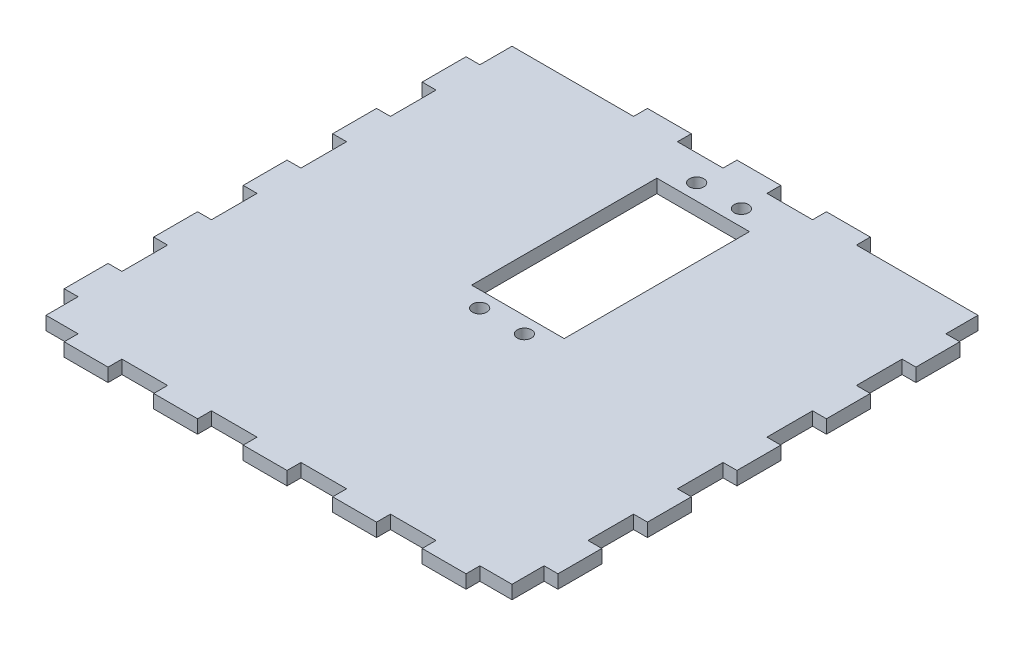
SolidWorks part; units mm, degrees
ref_plane "Front Plane" through (0, 0, 0) normal (0, 0, 1) x (1, 0, 0)
ref_plane "Top Plane" through (0, 0, 0) normal (0, 1, 0) x (1, 0, 0)
ref_plane "Right Plane" through (0, 0, 0) normal (1, 0, 0) x (0, 0, -1)
sketch "Sketch1" plane through (0, 0, 0) normal (0, 1, 0) x (1, 0, 0)
  line L0 (0, 0) -> (0, 21) construction
  line L1 (-10.05, 30.75) -> (-10.05, -10.05) construction
  line L2 (-10.05, -10.05) -> (10.05, -10.05) construction
  line L3 (10.05, 30.75) -> (10.05, -10.05) construction
  line L4 (-10.05, 30.75) -> (10.05, 30.75) construction
  line L5 (-10.05, 30.75) -> (-10.05, -10.05) construction
  line L6 (-10.05, -10.05) -> (10.05, -10.05) construction
  line L7 (10.05, 30.75) -> (10.05, -10.05) construction
  line L8 (-10.05, 30.75) -> (10.05, 30.75) construction
  line L9 (-10.35, 31.05) -> (10.35, 31.05)
  line L10 (10.35, 31.05) -> (10.35, -10.35)
  line L11 (-10.35, -10.35) -> (10.35, -10.35)
  line L12 (-10.35, 31.05) -> (-10.35, -10.35)
  line L13 (55.1722, 43.5014) -> (55.1722, -66.843) construction
  line L14 (55.1722, 43.5014) -> (55.1722, -66.843)
  line L15 (-55.1722, 43.5014) -> (-55.1722, -66.843) construction
  line L16 (-55.1722, 43.5014) -> (-55.1722, -66.843)
  line L17 (-55.1722, -66.843) -> (55.1722, -66.843) construction
  line L18 (-55.1722, -66.843) -> (55.1722, -66.843)
  line L20 (-55.1722, 43.5014) -> (55.1722, 43.5014) construction
  line L21 (-55.1722, 43.5014) -> (55.1722, 43.5014)
  circle A0 centre (0, 0) radius 21 construction
  circle A1 centre (0, 0) radius 21 construction
  circle A2 centre (-5, -13.9) radius 2 construction
  circle A3 centre (5, -13.9) radius 2 construction
  circle A4 centre (-5, 34.6) radius 2 construction
  circle A5 centre (5, 34.6) radius 2 construction
  circle A6 centre (5, -13.9) radius 2 construction
  circle A7 centre (-5, -13.9) radius 2 construction
  circle A8 centre (-5, 34.6) radius 2 construction
  circle A9 centre (5, 34.6) radius 2 construction
  circle A10 centre (-5, 34.6) radius 1.6
  circle A11 centre (5, 34.6) radius 1.6
  circle A12 centre (5, -13.9) radius 1.6
  circle A13 centre (-5, -13.9) radius 1.6
  dimension "D2" = 3.2
  dimension "D1" = 0.3
extrude "Boss-Extrude1" add sketch "Sketch1" along normal up to vertex (3 mm away)
sketch "Sketch2" plane through (0, 0, 0) normal (0, 1, 0) x (1, 0, 0)
  line L0 (-55.1722, -6.6708) -> (-52.1722, -6.6708)
  line L1 (-55.1722, -16.6708) -> (-52.1722, -16.6708)
  line L2 (-55.1722, 3.3292) -> (-52.1722, 3.3292)
  line L3 (-55.1722, 13.3292) -> (-52.1722, 13.3292)
  line L4 (-55.1722, 43.5014) -> (-55.1722, -66.843) construction
  line L5 (-55.1722, 43.5014) -> (55.1722, 43.5014)
  line L6 (-55.1722, 43.5014) -> (-55.1722, -66.843)
  line L7 (-55.1722, -66.843) -> (55.1722, -66.843)
  line L8 (55.1722, 43.5014) -> (55.1722, -66.843)
  line L9 (-55.1722, 43.5014) -> (55.1722, 43.5014) construction
  line L10 (55.1722, 43.5014) -> (55.1722, -66.843) construction
  line L11 (-55.1722, -66.843) -> (55.1722, -66.843) construction
  line L12 (0, -11.6708) -> (0, 43.5014) construction
  line L13 (-55.1722, -11.6708) -> (0, -11.6708) construction
  line L14 (-52.1722, 40.5014) -> (-52.1722, -63.843) construction
  line L15 (-52.1722, -63.843) -> (52.1722, -63.843) construction
  line L16 (52.1722, -63.843) -> (52.1722, 40.5014) construction
  line L17 (52.1722, 40.5014) -> (-52.1722, 40.5014) construction
  line L18 (-55.1722, 43.5014) -> (0, -11.6708) construction
  line L19 (-52.1722, -63.843) -> (-55.1722, -63.843) construction
  line L20 (-32.0585, 80.0877) -> (-35.0585, 80.0877) construction
  line L21 (-53.6722, -6.6708) -> (-53.6722, -16.6708) construction
  line L22 (-53.6722, -6.6708) -> (-53.6722, 3.3292) construction
  line L23 (-53.6722, 3.3292) -> (-53.6722, 13.3292) construction
  line L24 (-55.1722, 23.3292) -> (-52.1722, 23.3292)
  line L25 (-55.1722, 33.3292) -> (-52.1722, 33.3292)
  line L26 (-53.6722, 13.3292) -> (-53.6722, 23.3292) construction
  line L27 (-53.6722, 23.3292) -> (-53.6722, 33.3292) construction
  line L28 (-55.1722, -16.6708) -> (-52.1722, -16.6708)
  line L29 (-55.1722, -26.6708) -> (-52.1722, -26.6708)
  line L30 (-55.1722, -36.6708) -> (-52.1722, -36.6708)
  line L31 (-55.1722, -46.6708) -> (-52.1722, -46.6708)
  line L32 (-55.1722, -56.6708) -> (-52.1722, -56.6708)
  line L33 (55.1722, 33.3292) -> (52.1722, 33.3292)
  line L34 (55.1722, 23.3292) -> (52.1722, 23.3292)
  line L35 (55.1722, 13.3292) -> (52.1722, 13.3292)
  line L36 (55.1722, 3.3292) -> (52.1722, 3.3292)
  line L37 (55.1722, -6.6708) -> (52.1722, -6.6708)
  line L38 (55.1722, -16.6708) -> (52.1722, -16.6708)
  line L39 (55.1722, -26.6708) -> (52.1722, -26.6708)
  line L40 (55.1722, -36.6708) -> (52.1722, -36.6708)
  line L41 (55.1722, -46.6708) -> (52.1722, -46.6708)
  line L42 (55.1722, -56.6708) -> (52.1722, -56.6708)
  line L43 (-5, 43.5014) -> (-5, 40.5014)
  line L44 (-45, 43.5014) -> (-45, 40.5014)
  line L45 (-35, 43.5014) -> (-35, 40.5014)
  line L46 (-25, 43.5014) -> (-25, 40.5014)
  line L47 (-15, 43.5014) -> (-15, 40.5014)
  line L48 (5, 43.5014) -> (5, 40.5014)
  line L49 (15, 43.5014) -> (15, 40.5014)
  line L50 (25, 43.5014) -> (25, 40.5014)
  line L51 (35, 43.5014) -> (35, 40.5014)
  line L52 (45, 43.5014) -> (45, 40.5014)
  line L53 (45, -66.843) -> (45, -63.843)
  line L54 (35, -66.843) -> (35, -63.843)
  line L55 (25, -66.843) -> (25, -63.843)
  line L56 (15, -66.843) -> (15, -63.843)
  line L57 (5, -66.843) -> (5, -63.843)
  line L58 (-5, -66.843) -> (-5, -63.843)
  line L59 (-15, -66.843) -> (-15, -63.843)
  line L60 (-25, -66.843) -> (-25, -63.843)
  line L61 (-35, -66.843) -> (-35, -63.843)
  line L62 (-45, -66.843) -> (-45, -63.843)
  dimension "D1" = 10
sketch "Sketch3" plane through (0, 0, 0) normal (0, 1, 0) x (1, 0, 0)
  line L0 (-55.2722, 43.6014) -> (-55.2722, 33.2292)
  line L1 (-55.2722, 3.4292) -> (-52.0722, 3.4292)
  line L2 (-55.2722, 3.4292) -> (-55.2722, -6.7708)
  line L3 (-55.2722, -6.7708) -> (-52.0722, -6.7708)
  line L4 (-52.0722, 3.4292) -> (-52.0722, -6.7708)
  line L5 (-55.2722, 23.4292) -> (-52.0722, 23.4292)
  line L6 (-55.2722, 23.4292) -> (-55.2722, 13.2292)
  line L7 (-55.2722, 13.2292) -> (-52.0722, 13.2292)
  line L8 (-52.0722, 23.4292) -> (-52.0722, 13.2292)
  line L9 (-55.2722, 33.2292) -> (-52.0722, 33.2292)
  line L10 (-52.0722, 33.2292) -> (-52.0722, 40.4014)
  line L11 (-55.1722, -6.6708) -> (-55.2722, -6.6708) construction
  line L12 (-55.1722, -6.6708) -> (-55.1722, -6.7708) construction
  line L13 (-55.1722, 3.3292) -> (-55.1722, 3.4292) construction
  line L14 (-55.1722, 13.3292) -> (-55.1722, 13.2292) construction
  line L15 (-55.1722, 23.3292) -> (-55.1722, 23.4292) construction
  line L16 (-55.1722, 33.3292) -> (-55.1722, 33.2292) construction
  line L17 (-55.1722, -6.6708) -> (-52.1722, -6.6708) construction
  line L18 (-52.1722, -6.6708) -> (-52.0722, -6.6708) construction
  line L19 (-55.1722, -11.6708) -> (0, -11.6708) construction
  line L20 (0, -11.6708) -> (0, 43.5014) construction
  line L21 (0, -11.6708) -> (-55.1722, 43.5014) construction
  line L22 (-15.1, 43.6014) -> (-15.1, 40.4014)
  line L23 (-15.1, 43.6014) -> (-4.9, 43.6014)
  line L24 (-4.9, 43.6014) -> (-4.9, 40.4014)
  line L25 (-15.1, 40.4014) -> (-4.9, 40.4014)
  line L26 (-35.1, 43.6014) -> (-35.1, 40.4014) construction
  line L27 (-35.1, 43.6014) -> (-24.9, 43.6014) construction
  line L28 (-24.9, 43.6014) -> (-24.9, 40.4014)
  line L29 (-35.1, 40.4014) -> (-24.9, 40.4014) construction
  line L30 (-44.9, 40.4014) -> (-52.0722, 40.4014) construction
  line L31 (-44.9, 43.6014) -> (-44.9, 40.4014) construction
  line L32 (-55.2722, 43.6014) -> (-44.9, 43.6014) construction
  line L33 (-15.1, -66.943) -> (-15.1, -63.743)
  line L34 (-15.1, -66.943) -> (-4.9, -66.943)
  line L35 (-4.9, -66.943) -> (-4.9, -63.743)
  line L36 (-15.1, -63.743) -> (-4.9, -63.743)
  line L37 (-35.1, -66.943) -> (-35.1, -63.743)
  line L38 (-35.1, -66.943) -> (-24.9, -66.943)
  line L39 (-24.9, -66.943) -> (-24.9, -63.743)
  line L40 (-35.1, -63.743) -> (-24.9, -63.743)
  line L41 (-55.2722, -56.5708) -> (-52.0722, -56.5708)
  line L42 (-55.2722, -66.943) -> (-55.2722, -56.5708)
  line L43 (-55.2722, -66.943) -> (-44.9, -66.943)
  line L44 (-44.9, -66.943) -> (-44.9, -63.743)
  line L45 (-44.9, -63.743) -> (-52.0722, -63.743)
  line L46 (-52.0722, -56.5708) -> (-52.0722, -63.743)
  line L47 (-55.2722, -26.7708) -> (-52.0722, -26.7708)
  line L48 (-55.2722, -26.7708) -> (-55.2722, -16.5708)
  line L49 (-55.2722, -16.5708) -> (-52.0722, -16.5708)
  line L50 (-52.0722, -26.7708) -> (-52.0722, -16.5708)
  line L51 (-55.2722, -46.7708) -> (-52.0722, -46.7708)
  line L52 (-55.2722, -46.7708) -> (-55.2722, -36.5708)
  line L53 (-55.2722, -36.5708) -> (-52.0722, -36.5708)
  line L54 (-52.0722, -46.7708) -> (-52.0722, -36.5708)
  line L55 (35.1, -63.743) -> (24.9, -63.743)
  line L56 (24.9, -66.943) -> (24.9, -63.743)
  line L57 (35.1, -66.943) -> (24.9, -66.943)
  line L58 (35.1, -66.943) -> (35.1, -63.743)
  line L59 (15.1, -63.743) -> (4.9, -63.743)
  line L60 (4.9, -66.943) -> (4.9, -63.743)
  line L61 (15.1, -66.943) -> (4.9, -66.943)
  line L62 (15.1, -66.943) -> (15.1, -63.743)
  line L63 (52.0722, -46.7708) -> (52.0722, -36.5708)
  line L64 (55.2722, -36.5708) -> (52.0722, -36.5708)
  line L65 (55.2722, -46.7708) -> (55.2722, -36.5708)
  line L66 (55.2722, -46.7708) -> (52.0722, -46.7708)
  line L67 (52.0722, -26.7708) -> (52.0722, -16.5708)
  line L68 (55.2722, -16.5708) -> (52.0722, -16.5708)
  line L69 (55.2722, -26.7708) -> (55.2722, -16.5708)
  line L70 (55.2722, -26.7708) -> (52.0722, -26.7708)
  line L71 (52.0722, -56.5708) -> (52.0722, -63.743)
  line L72 (44.9, -63.743) -> (52.0722, -63.743)
  line L73 (44.9, -66.943) -> (44.9, -63.743)
  line L74 (55.2722, -66.943) -> (44.9, -66.943)
  line L75 (55.2722, -66.943) -> (55.2722, -56.5708)
  line L76 (55.2722, -56.5708) -> (52.0722, -56.5708)
  line L77 (55.2722, 3.4292) -> (52.0722, 3.4292)
  line L78 (55.2722, 3.4292) -> (55.2722, -6.7708)
  line L79 (55.2722, -6.7708) -> (52.0722, -6.7708)
  line L80 (52.0722, 3.4292) -> (52.0722, -6.7708)
  line L81 (55.2722, 23.4292) -> (52.0722, 23.4292)
  line L82 (55.2722, 23.4292) -> (55.2722, 13.2292)
  line L83 (55.2722, 13.2292) -> (52.0722, 13.2292)
  line L84 (52.0722, 23.4292) -> (52.0722, 13.2292)
  line L85 (35.1, 40.4014) -> (24.9, 40.4014) construction
  line L86 (24.9, 43.6014) -> (24.9, 40.4014)
  line L87 (35.1, 43.6014) -> (24.9, 43.6014) construction
  line L88 (35.1, 43.6014) -> (35.1, 40.4014) construction
  line L89 (15.1, 40.4014) -> (4.9, 40.4014)
  line L90 (4.9, 43.6014) -> (4.9, 40.4014)
  line L91 (15.1, 43.6014) -> (4.9, 43.6014)
  line L92 (15.1, 43.6014) -> (15.1, 40.4014)
  line L93 (55.2722, 43.6014) -> (44.9, 43.6014) construction
  line L94 (44.9, 43.6014) -> (44.9, 40.4014) construction
  line L95 (44.9, 40.4014) -> (52.0722, 40.4014) construction
  line L96 (52.0722, 33.2292) -> (52.0722, 40.4014)
  line L97 (55.2722, 33.2292) -> (52.0722, 33.2292)
  line L98 (55.2722, 43.6014) -> (55.2722, 33.2292)
  line L99 (-52.0722, 40.4014) -> (-24.9, 40.4014)
  line L100 (-24.9, 43.6014) -> (-55.2722, 43.6014)
  line L101 (24.9, 40.4014) -> (52.0722, 40.4014)
  line L102 (55.2722, 43.6014) -> (24.9, 43.6014)
  dimension "D1" = 0.1
extrude "Cut-Extrude1" cut sketch "Sketch3" along normal through all
